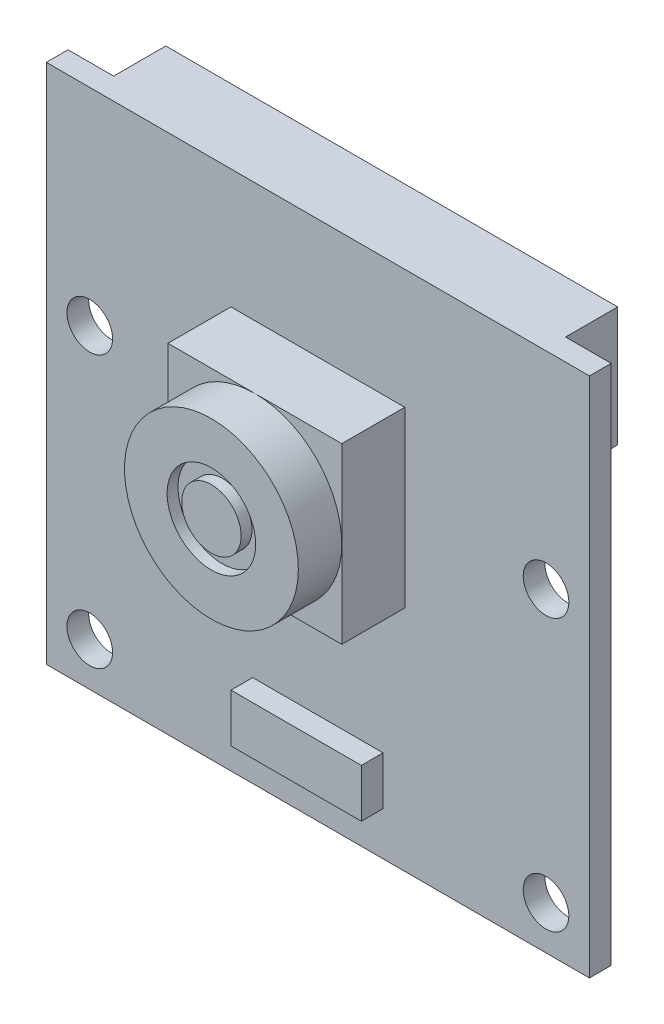
SolidWorks part; units mm, degrees
ref_plane "Front Plane" through (0, 0, 0) normal (0, 0, 1) x (1, 0, 0)
ref_plane "Top Plane" through (0, 0, 0) normal (0, 1, 0) x (1, 0, 0)
ref_plane "Right Plane" through (0, 0, 0) normal (1, 0, 0) x (0, 0, -1)
sketch "Sketch1" plane through (0, 0, 0) normal (0, 0, 1) x (1, 0, 0)
  line L0 (0, 18.1386) -> (0, -22.6892) construction
  line L1 (-12.5, 12) -> (12.5, 12)
  line L2 (-12.5, 12) -> (-12.5, -12)
  line L3 (-12.5, -12) -> (12.5, -12)
  line L4 (12.5, 12) -> (12.5, -12)
  circle A0 centre (-10.5, 2.5) radius 1.05
  circle A1 centre (-10.5, -10) radius 1.05
  circle A2 centre (10.5, -10) radius 1.05
  circle A3 centre (10.5, 2.5) radius 1.05
  point P0 (0, 0)
  dimension "D3" = 2.1
  dimension "D1" = 24
  dimension "D2" = 25
  dimension "D4" = 9.5
  dimension "D5" = 2
  dimension "D6" = 12.5
extrude "Boss-Extrude1" add sketch "Sketch1" along normal blind 1
sketch "Sketch2" plane through (0, 0, 0) normal (0, 0, -1) x (-1, 0, 0)
  line L0 (-12.5, 12) -> (12.5, 12) construction
  line L1 (10.4, 12) -> (-10.4, 12)
  line L2 (10.4, 12) -> (10.4, 6.5)
  line L3 (10.4, 6.5) -> (-10.4, 6.5)
  line L4 (-10.4, 12) -> (-10.4, 6.5)
  line L5 (-12.5, -12) -> (-12.5, 12) construction
  point P8 (-10.4, 9.25)
  dimension "D1" = 5.5
  dimension "D2" = 20.8
  dimension "D3" = 2.1
extrude "Boss-Extrude2" add sketch "Sketch2" along normal blind 2.4
sketch "Sketch3" plane through (0, 0, 1) normal (0, 0, 1) x (1, 0, 0)
  line L0 (12.5, 12) -> (-12.5, 12) construction
  line L1 (-4, -1.5) -> (4, -1.5)
  line L2 (-4, -1.5) -> (-4, 6.5)
  line L3 (-4, 6.5) -> (4, 6.5)
  line L4 (4, -1.5) -> (4, 6.5)
  line L5 (12.5, -12) -> (12.5, 12) construction
  dimension "D1" = 8
  dimension "D2" = 8
  dimension "D3" = 5.5
  dimension "D4" = 8.5
extrude "Boss-Extrude3" add sketch "Sketch3" along normal blind 4.9
sketch "Sketch6" plane through (0, 0, 5.9) normal (0, 0, 1) x (1, 0, 0)
  line L0 (4, 6.5) -> (-4, 6.5) construction
  line L2 (4, -1.5) -> (4, 6.5) construction
  line L4 (-4, -1.5) -> (4, -1.5)
  line L5 (-4, -1.5) -> (-4, 6.5)
  line L6 (-4, 6.5) -> (4, 6.5)
  line L7 (4, -1.5) -> (4, 6.5)
  circle A0 centre (0, 2.5) radius 4
  line M1 (-4, 6.5) -> (-4, -1.5)
  line M2 (-4, -1.5) -> (4, -1.5)
  line M3 (4, -1.5) -> (4, 6.5)
  line M4 (4, 6.5) -> (-4, 6.5)
  dimension "D1" = 8
  dimension "D2" = 4
  dimension "D3" = 4
extrude "Cut-Extrude3" cut sketch "Sketch6" against normal blind 2 contours A0 L6 M1 | A0 L7 M4 | A0 L4 M3 | A0 L5 M2
sketch "Sketch7" plane through (0, 0, 5.9) normal (0, 0, 1) x (1, 0, 0)
  circle A0 centre (0, 2.5) radius 1.3678
  circle A1 centre (0, 2.5) radius 2.0382
extrude "Cut-Extrude4" cut sketch "Sketch7" against normal blind 0.5
sketch "Sketch8" plane through (0, 0, 1) normal (0, 0, 1) x (1, 0, 0)
  line L1 (-3, -10) -> (3, -10)
  line L2 (-3, -10) -> (-3, -7.7754)
  line L3 (-3, -7.7754) -> (3, -7.7754)
  line L4 (3, -10) -> (3, -7.7754)
  point P4 (0, 0)
  dimension "D1" = 6
  dimension "D2" = 1
extrude "Boss-Extrude4" add sketch "Sketch8" along normal blind 1
